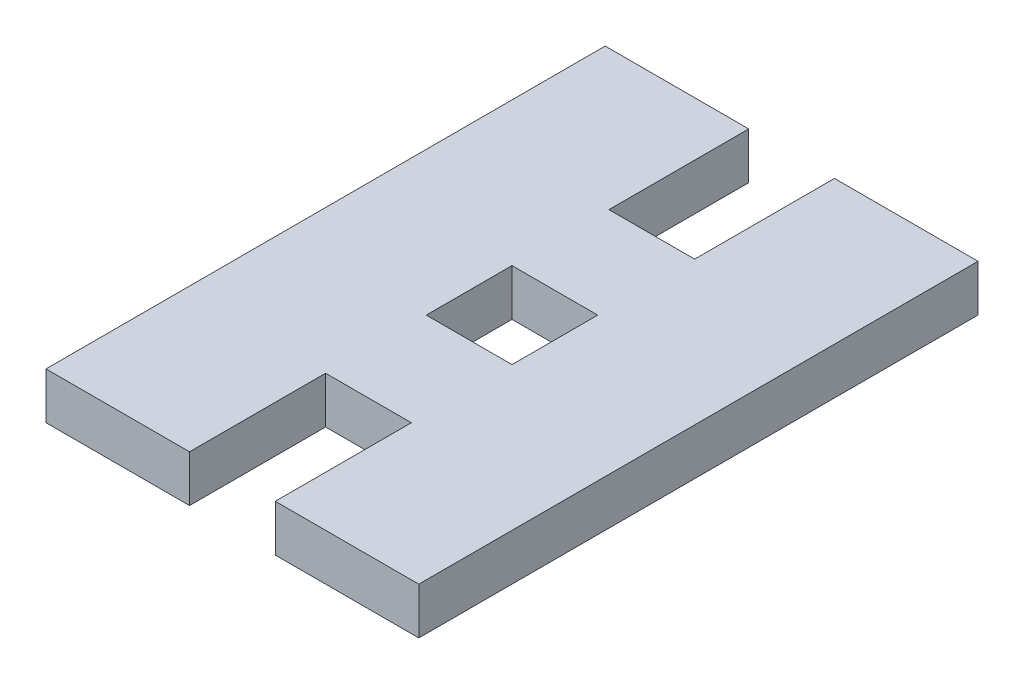
SolidWorks part; units mm, degrees
ref_plane "Front Plane" through (0, 0, 0) normal (0, 0, 1) x (1, 0, 0)
ref_plane "Top Plane" through (0, 0, 0) normal (0, 1, 0) x (1, 0, 0)
ref_plane "Right Plane" through (0, 0, 0) normal (1, 0, 0) x (0, 0, -1)
sketch "Sketch1" plane through (0, 0, 0) normal (0, 1, 0) x (1, 0, 0)
  line L0 (0, 38.1) -> (25.4, 38.1)
  line L1 (0, 0) -> (25.4, 0)
  line L2 (0, 0) -> (0, 38.1)
  line L3 (9.779, 0) -> (15.621, 0)
  line L4 (25.4, 0) -> (25.4, 38.1)
  line L5 (9.779, 0) -> (9.779, 9.271)
  line L6 (9.779, 9.271) -> (15.621, 9.271)
  line L7 (15.621, 0) -> (15.621, 9.271)
  line L8 (9.779, 16.129) -> (15.621, 16.129)
  line L9 (9.779, 16.129) -> (9.779, 21.971)
  line L10 (9.779, 21.971) -> (15.621, 21.971)
  line L11 (15.621, 16.129) -> (15.621, 21.971)
  line L12 (9.779, 38.1) -> (15.621, 38.1)
  line L13 (9.779, 38.1) -> (9.779, 28.575)
  line L14 (9.779, 28.575) -> (15.621, 28.575)
  line L15 (15.621, 38.1) -> (15.621, 28.575)
  point P6 (12.7, 0)
  point P18 (9.779, 19.05)
  point P19 (0, 19.05)
  point P20 (12.7, 9.271)
  dimension "D1" = 38.1
  dimension "D2" = 25.4
  dimension "D3" = 9.271
  dimension "D4" = 5.842
  dimension "D5" = 9.525
  dimension "D6" = 5.842
extrude "Boss-Extrude1" add sketch "Sketch1" along normal blind 3.175 contours L0 L15 L14 L13 L2 L1 L5 L6 L7 L4 L11 L8 L9 L10
